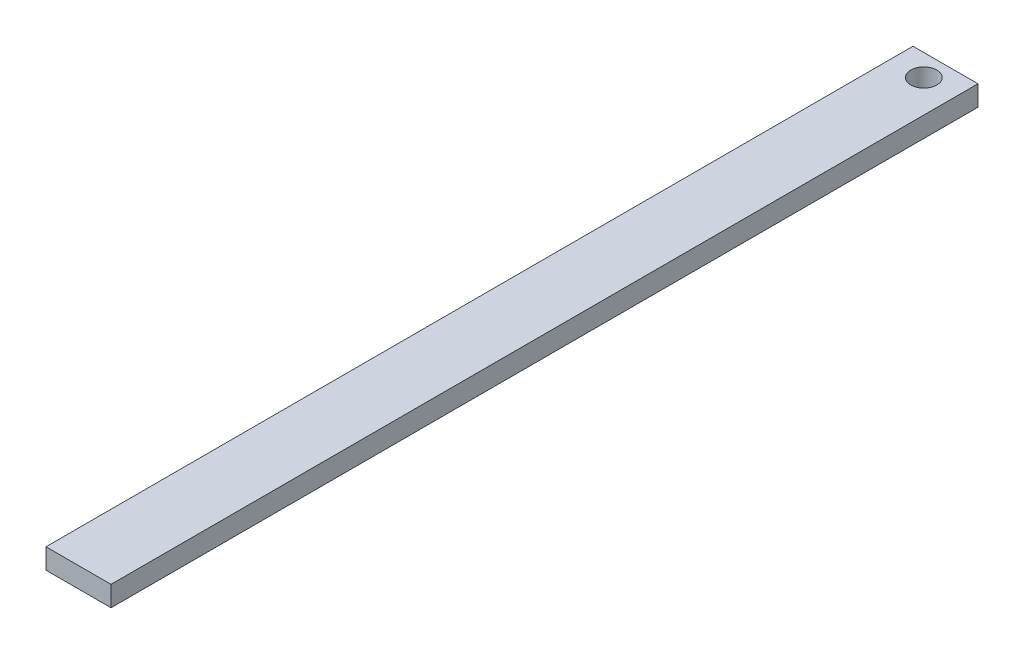
SolidWorks part; units mm, degrees
ref_plane "Front Plane" through (0, 0, 0) normal (0, 0, 1) x (1, 0, 0)
ref_plane "Top Plane" through (0, 0, 0) normal (0, 1, 0) x (1, 0, 0)
ref_plane "Right Plane" through (0, 0, 0) normal (1, 0, 0) x (0, 0, -1)
sketch "Sketch1" plane through (0, 0, 0) normal (0, 0, 1) x (1, 0, 0)
  line L0 (0, 0) -> (0, 2.3813)
  line L1 (0, 2.3813) -> (7.62, 2.3813)
  line L2 (7.62, 2.3813) -> (7.62, 0)
  line L3 (7.62, 0) -> (0, 0)
  dimension "D1" = 2.3813
  dimension "D2" = 7.62
extrude "Boss-Extrude1" add sketch "Sketch1" along normal blind 101.6
sketch "Sketch2" plane through (0, 2.3813, 0) normal (0, 1, 0) x (1, 0, 0)
  line L0 (3.81, 0) -> (3.81, -2.54)
  line L1 (7.62, 0) -> (0, 0) construction
  circle A0 centre (3.81, -2.54) radius 1.524
  dimension "D2" = 3.048
  dimension "D1" = 2.54
extrude "Cut-Extrude1" cut sketch "Sketch2" against normal through all
